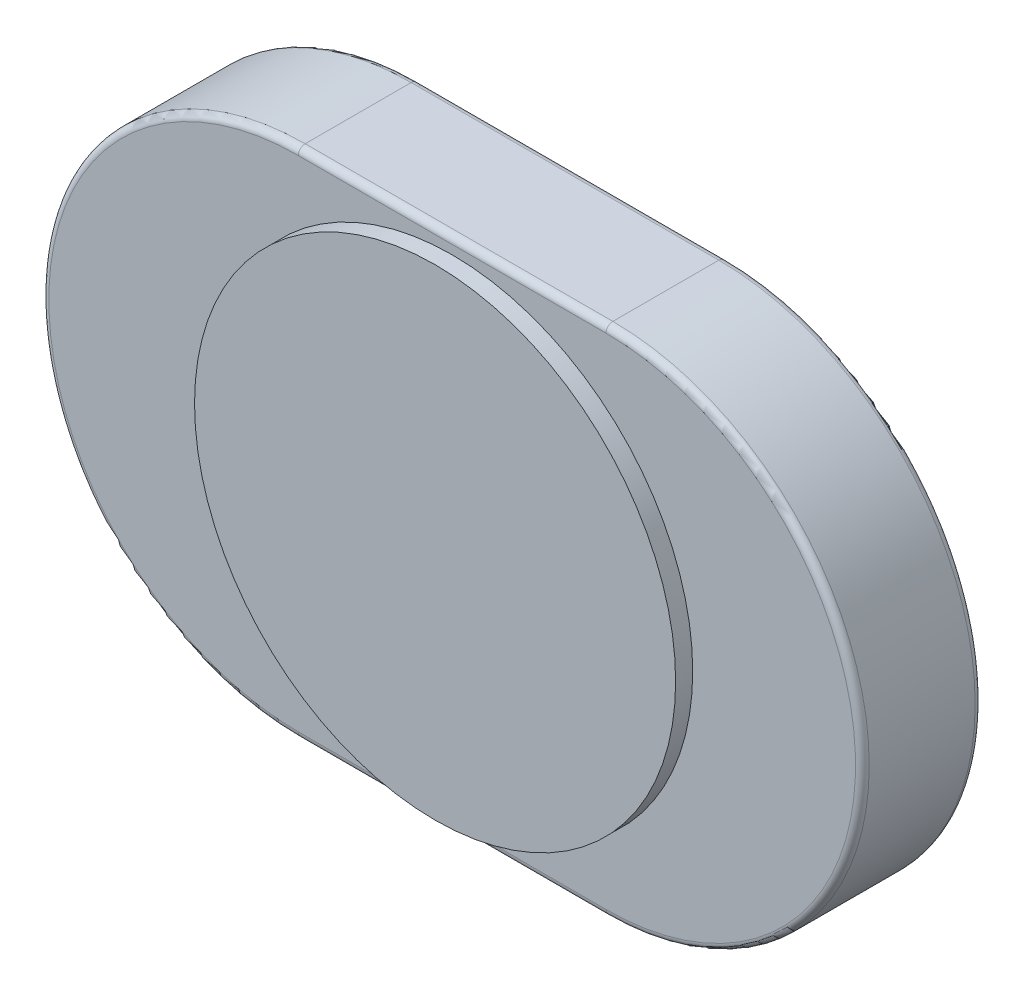
SolidWorks part; units mm, degrees
ref_plane "Front Plane" through (0, 0, 0) normal (0, 0, 1) x (1, 0, 0)
ref_plane "Top Plane" through (0, 0, 0) normal (0, 1, 0) x (1, 0, 0)
ref_plane "Right Plane" through (0, 0, 0) normal (1, 0, 0) x (0, 0, -1)
sketch "Sketch1" plane through (0, 0, 0) normal (0, 0, 1) x (1, 0, 0)
  line L1 (-4.5, -7.5) -> (4.5, -7.5)
  line L2 (-4.5, -7.5) -> (-4.5, 7.5) construction
  line L3 (-4.5, 7.5) -> (4.5, 7.5)
  line L4 (4.5, -7.5) -> (4.5, 7.5) construction
  line L5 (-4.5, -7.5) -> (4.5, 7.5) construction
  line L6 (-4.5, 7.5) -> (4.5, -7.5) construction
  arc A0 (-4.5, 7.5) -> (-4.5, -7.5) centre (-4.5, 0) ccw
  arc A1 (4.5, 7.5) -> (4.5, -7.5) centre (4.5, 0) cw
  point P0 (0, 0)
  dimension "D1" = 15
  dimension "D2" = 9
extrude "Boss-Extrude1" add sketch "Sketch1" along normal blind 3.5
sketch "Sketch2" plane through (0, 0, 3.5) normal (0, 0, 1) x (1, 0, 0)
  circle A0 centre (0, 0) radius 7.037
extrude "Boss-Extrude2" add sketch "Sketch2" along normal blind 0.5
fillet "Fillet1" radius 0.2 8 edges at (0, 7.5, 0) (12, 0, 0) (0, -7.5, 0) (0, 7.5, 3.5) (12, 0, 3.5) (0, -7.5, 3.5) (-12, 0, 0) (-12, 0, 3.5)
